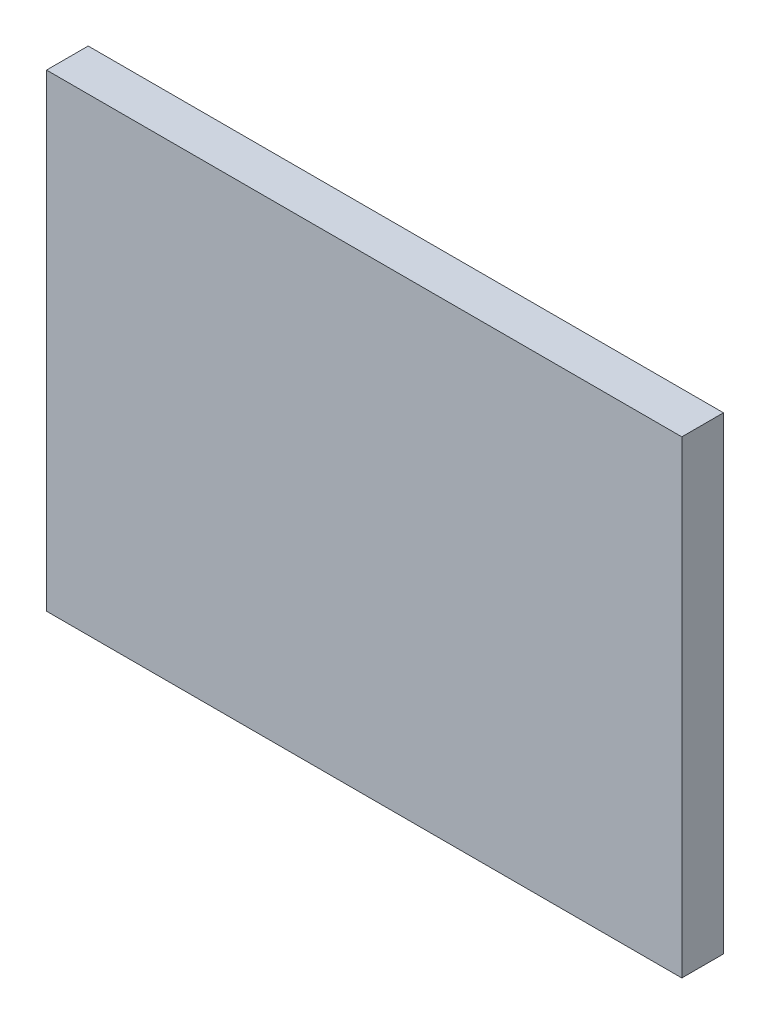
SolidWorks part; units mm, degrees
material "ABS"
ref_plane "Front Plane" through (0, 0, 0) normal (0, 0, 1) x (1, 0, 0)
ref_plane "Top Plane" through (0, 0, 0) normal (0, 1, 0) x (1, 0, 0)
ref_plane "Right Plane" through (0, 0, 0) normal (1, 0, 0) x (0, 0, -1)
sketch "Sketch1" plane through (0, 0, 0) normal (0, 0, 1) x (1, 0, 0)
  line L1 (0, 0) -> (61, 0)
  line L2 (0, 0) -> (0, 45)
  line L3 (0, 45) -> (61, 45)
  line L4 (61, 0) -> (61, 45)
  dimension "D1" = 61
  dimension "D2" = 45
extrude "Boss-Extrude1" add sketch "Sketch1" along normal blind 4
